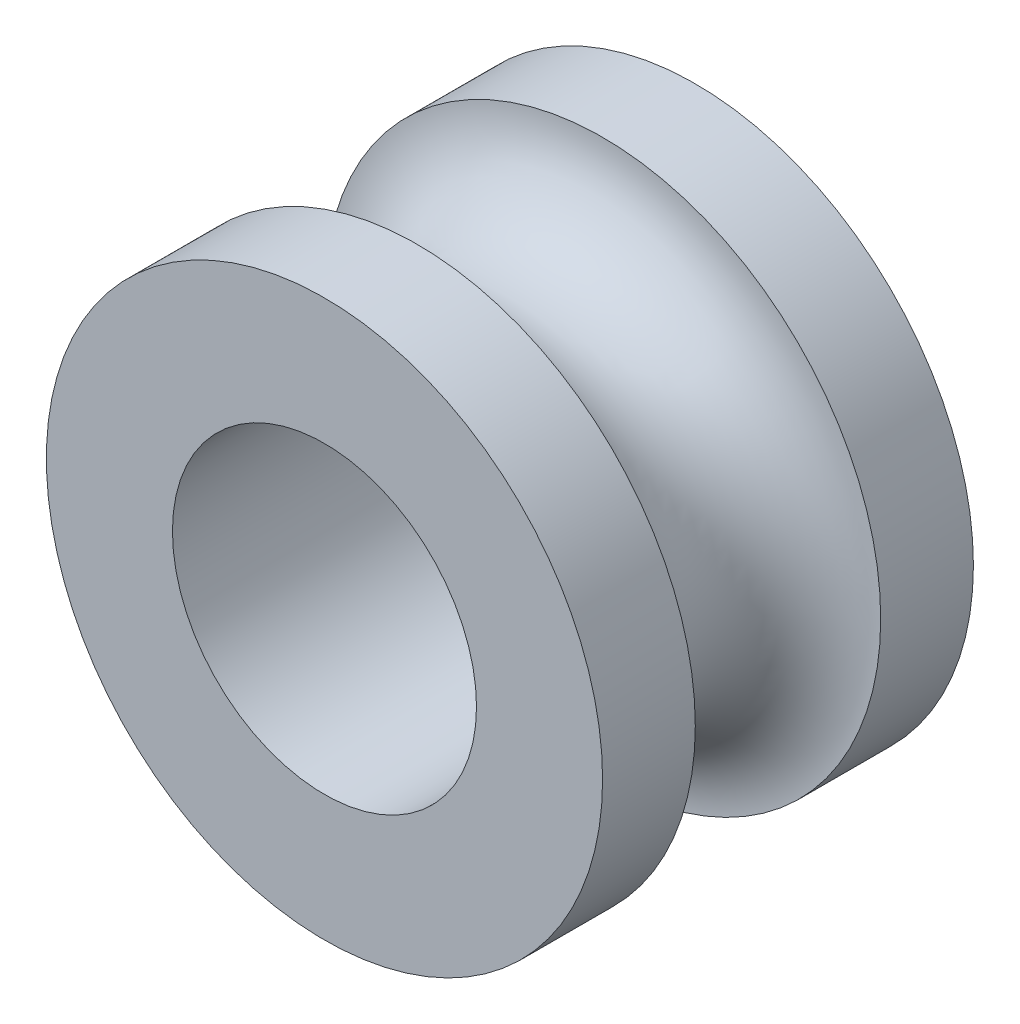
SolidWorks part; units mm, degrees
ref_plane "Front Plane" through (0, 0, 0) normal (0, 0, 1) x (1, 0, 0)
ref_plane "Top Plane" through (0, 0, 0) normal (0, 1, 0) x (1, 0, 0)
ref_plane "Right Plane" through (0, 0, 0) normal (1, 0, 0) x (0, 0, -1)
sketch "Sketch1" plane through (0, 0, 0) normal (0, 0, 1) x (1, 0, 0)
  circle A0 centre (0, 0) radius 3.75
  circle A1 centre (0, 0) radius 2.05
  dimension "D1" = 7.5
  dimension "D2" = 4.1
extrude "Boss-Extrude1" add sketch "Sketch1" along normal mid plane 5
ref_plane "Plane1" through (0, 0, 0) normal (0, 0, 1) x (1, 0, 0)
sketch "Sketch2" plane through (0, 0, 0) normal (0, 0, 1) x (1, 0, 0)
  circle A0 centre (0, 0) radius 3.75
  circle A1 centre (0, 0) radius 3.75 construction
sweep "Cut-Sweep1" cut path "Sketch2" circular profile diameter 2.5 parameters "D3"=2.5
